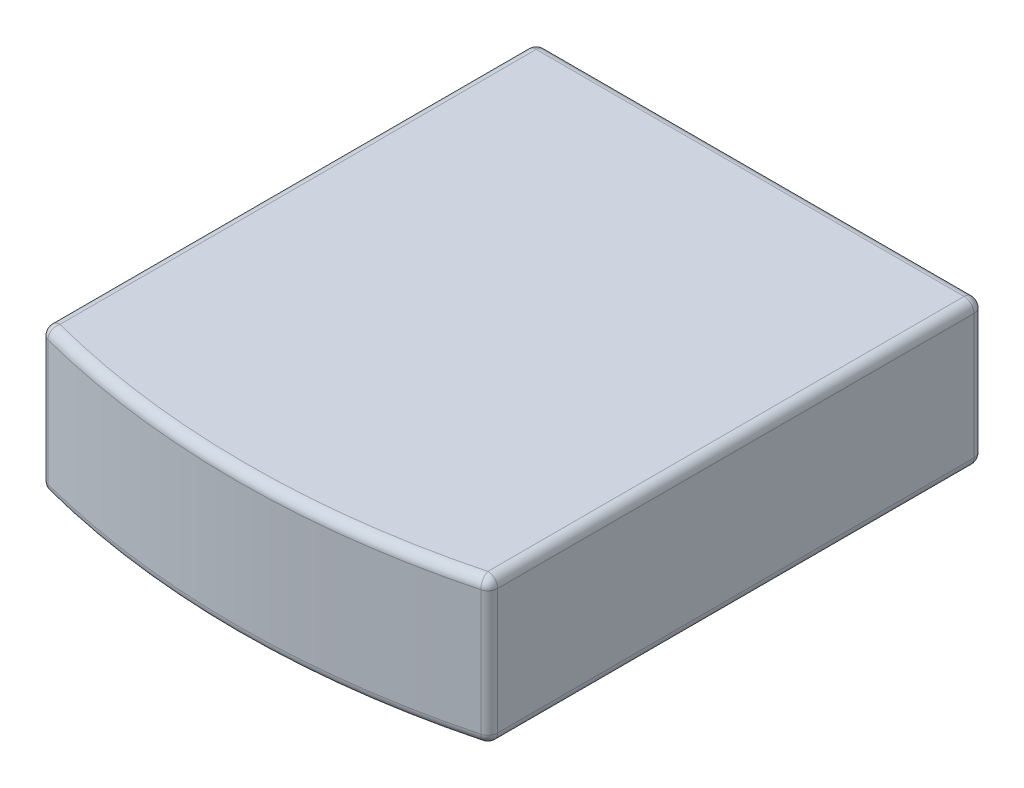
SolidWorks part; units mm, degrees
ref_plane "Front Plane" through (0, 0, 0) normal (0, 0, 1) x (1, 0, 0)
ref_plane "Top Plane" through (0, 0, 0) normal (0, 1, 0) x (1, 0, 0)
ref_plane "Right Plane" through (0, 0, 0) normal (1, 0, 0) x (0, 0, -1)
sketch "Sketch1" plane through (0, 0, 0) normal (0, 0, 1) x (1, 0, 0)
  line L0 (55, 0) -> (-55, 0) construction
  line L1 (-3.4, 1.1) -> (3.4, 1.1)
  line L2 (-3.4, 1.1) -> (-3.4, -1.1)
  line L3 (-3.4, -1.1) -> (3.4, -1.1)
  line L4 (3.4, 1.1) -> (3.4, -1.1)
  line L5 (0, -55) -> (0, 55) construction
  dimension "D1" = 2.2
  dimension "D2" = 6.8
  dimension "D3" = 1.1
  dimension "D4" = 3.4
extrude "Boss-Extrude1" add sketch "Sketch1" along normal blind 8
sketch "Sketch2" plane through (0, 1.1, 0) normal (0, 1, 0) x (1, 0, 0)
  line L0 (-3.4, -8) -> (-3.4, 0) construction
  line L1 (3.4, -8) -> (3.4, 0) construction
  line L2 (3.4, -8) -> (-3.4, -8) construction
  line L3 (-3.4, -7.5) -> (-4.3384, -8.75)
  line L4 (-4.3384, -8.75) -> (5.304, -8.9718)
  line L5 (5.304, -8.9718) -> (3.4, -7.5)
  arc A0 (-3.4, -7.5) -> (3.4, -7.5) centre (0, 5.0475) ccw
  dimension "D3" = 13
  dimension "D1" = 0.5
  dimension "D2" = 0.5
extrude "Cut-Extrude1" cut sketch "Sketch2" against normal blind 8
fillet "Fillet1" radius 0.15 12 edges at (-3.4, -1.1, 3.75) (3.4, -1.1, 3.75) (3.4, 1.1, 3.75) (-3.4, 1.1, 3.75) (0, 1.1, 0) (3.4, 0, 0) (0, -1.1, 0) (-3.4, 0, 0) (0, -1.1, 7.9525) (3.4, 0, 7.5) (-3.4, 0, 7.5) (0, 1.1, 7.9525)
